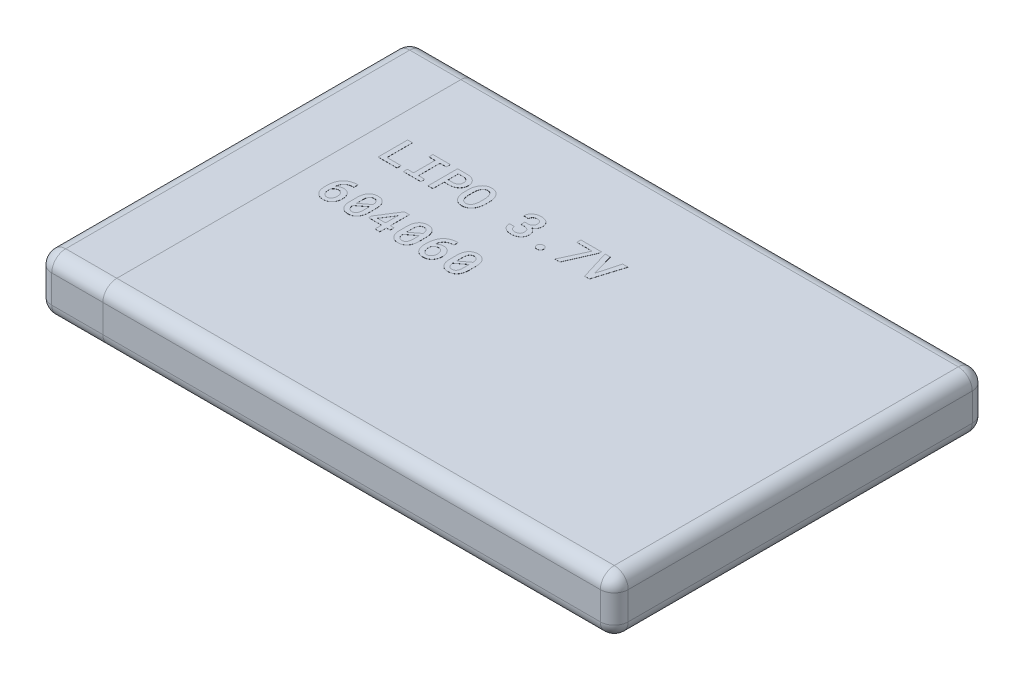
SolidWorks part; units mm, degrees
ref_plane "Front Plane" through (0, 0, 0) normal (0, 0, 1) x (1, 0, 0)
ref_plane "Top Plane" through (0, 0, 0) normal (0, 1, 0) x (1, 0, 0)
ref_plane "Right Plane" through (0, 0, 0) normal (1, 0, 0) x (0, 0, -1)
sketch "Sketch1" plane through (0, 0, 0) normal (0, 1, 0) x (1, 0, 0)
  line L1 (-19.6052, -30.8717) -> (35.3948, -30.8717)
  line L2 (-19.6052, -30.8717) -> (-19.6052, 9.1283)
  line L3 (-19.6052, 9.1283) -> (35.3948, 9.1283)
  line L4 (35.3948, -30.8717) -> (35.3948, 9.1283)
  dimension "D1" = 55
  dimension "D2" = 40
extrude "Boss-Extrude1" add sketch "Sketch1" along normal blind 6
sketch "Sketch2" plane through (-19.6052, 0, 0) normal (-1, 0, 0) x (0, 0, 1)
  line L1 (-9.1283, 6) -> (30.8717, 6)
  line L2 (-9.1283, 6) -> (-9.1283, 0)
  line L3 (-9.1283, 0) -> (30.8717, 0)
  line L4 (30.8717, 6) -> (30.8717, 0)
extrude "Boss-Extrude3" add sketch "Sketch2" along normal blind 7 separate body
fillet "Fillet1" radius 1.5 8 edges at (35.3948, 6, 10.8717) (35.3948, 0, 10.8717) (7.8948, 0, 30.8717) (7.8948, 0, -9.1283) (7.8948, 6, -9.1283) (7.8948, 6, 30.8717) (35.3948, 3, -9.1283) (35.3948, 3, 30.8717)
fillet "Fillet2" radius 1.5 8 edges at (-26.6052, 3, 30.8717) (-23.1052, 6, 30.8717) (-23.1052, 0, 30.8717) (-23.1052, 0, -9.1283) (-26.6052, 0, 10.8717) (-26.6052, 6, 10.8717) (-26.6052, 3, -9.1283) (-23.1052, 6, -9.1283)
sketch "Sketch3" plane through (0, 6, 0) normal (0, 1, 0) x (1, 0, 0)
  text T0 "<b>LIPO 3.7V</b>\r\n<b>604060</b>" font "Roboto Mono Medium" height 3.175
  point P1 (0, 0)
extrude "Boss-Extrude5" add sketch "Sketch3" along normal blind 0.01 separate body
